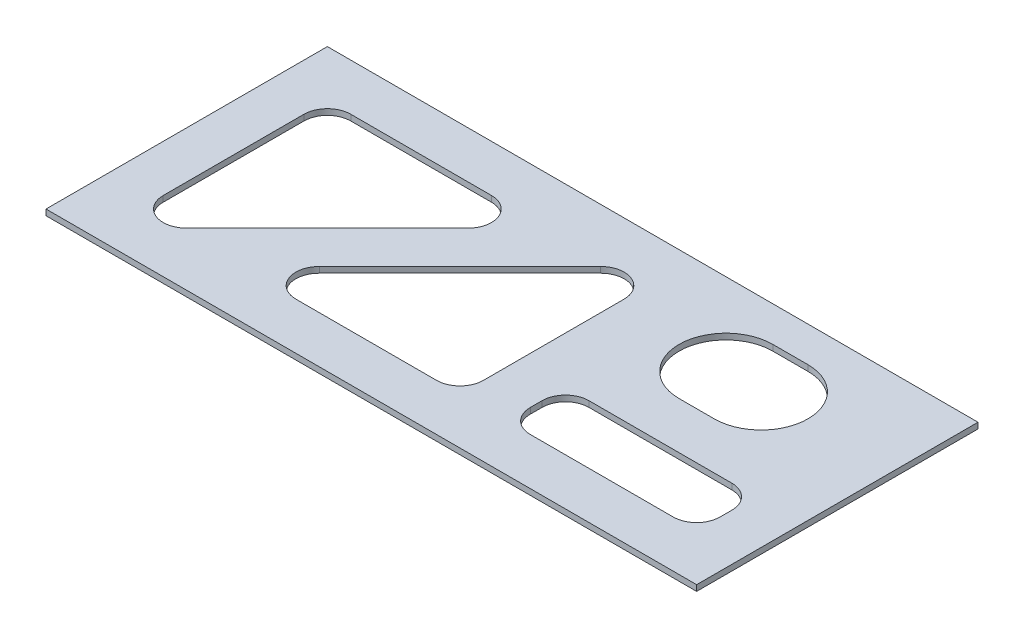
SolidWorks part; units mm, degrees
material "ASTM A36 Steel"
ref_plane "Front Plane" through (0, 0, 0) normal (0, 0, 1) x (1, 0, 0)
ref_plane "Top Plane" through (0, 0, 0) normal (0, 1, 0) x (1, 0, 0)
ref_plane "Right Plane" through (0, 0, 0) normal (1, 0, 0) x (0, 0, -1)
sketch "Sketch1" plane through (0, 0, 0) normal (0, 1, 0) x (1, 0, 0)
  line L1 (176.2125, 76.2) -> (-176.2125, 76.2)
  line L2 (176.2125, 76.2) -> (176.2125, -76.2)
  line L3 (176.2125, -76.2) -> (-176.2125, -76.2)
  line L4 (-176.2125, 76.2) -> (-176.2125, -76.2)
  line L5 (176.2125, 76.2) -> (-176.2125, -76.2) construction
  line L6 (176.2125, -76.2) -> (-176.2125, 76.2) construction
  point P0 (0, 0)
  dimension "D1" = 152.4
  dimension "D2" = 352.425
extrude "Boss-Extrude1" add sketch "Sketch1" along normal mid plane 3.175
sketch "Sketch2" plane through (0, 1.5875, 0) normal (0, 1, 0) x (1, 0, 0)
  line L0 (103.1875, 31.75) -> (84.1375, 31.75) construction
  line L1 (103.1875, 6.35) -> (84.1375, 6.35)
  line L2 (103.1875, 57.15) -> (84.1375, 57.15)
  line L4 (176.2125, -76.2) -> (176.2125, 76.2) construction
  line L5 (176.2125, 76.2) -> (-176.2125, 76.2) construction
  line L6 (-138.1125, 50.8) -> (-61.9125, 50.8)
  line L7 (-52.9322, 29.1197) -> (-129.1322, -47.0803)
  line L8 (-150.8125, -38.1) -> (-150.8125, 38.1)
  line L9 (-176.2125, 76.2) -> (-176.2125, -76.2) construction
  line L10 (-66.2705, -50.8) -> (9.9295, -50.8)
  line L11 (22.6295, -38.1) -> (22.6295, 38.1)
  line L12 (0.9493, 47.0803) -> (-75.2507, -29.1197)
  line L13 (-176.2125, -76.2) -> (176.2125, -76.2) construction
  line L14 (60.7295, -50.8) -> (138.1125, -50.8)
  line L15 (150.8125, -38.1) -> (150.8125, -31.75)
  line L16 (138.1125, -19.05) -> (60.7295, -19.05)
  line L17 (48.0295, -31.75) -> (48.0295, -38.1)
  arc A0 (103.1875, 6.35) -> (103.1875, 57.15) centre (103.1875, 31.75) ccw
  arc A1 (84.1375, 57.15) -> (84.1375, 6.35) centre (84.1375, 31.75) ccw
  arc A2 (-61.9125, 50.8) -> (-52.9322, 29.1197) centre (-61.9125, 38.1) cw
  arc A3 (-129.1322, -47.0803) -> (-150.8125, -38.1) centre (-138.1125, -38.1) cw
  arc A4 (-150.8125, 38.1) -> (-138.1125, 50.8) centre (-138.1125, 38.1) cw
  arc A5 (9.9295, -50.8) -> (22.6295, -38.1) centre (9.9295, -38.1) ccw
  arc A6 (22.6295, 38.1) -> (0.9493, 47.0803) centre (9.9295, 38.1) ccw
  arc A7 (-75.2507, -29.1197) -> (-66.2705, -50.8) centre (-66.2705, -38.1) ccw
  arc A8 (138.1125, -50.8) -> (150.8125, -38.1) centre (138.1125, -38.1) ccw
  arc A9 (150.8125, -31.75) -> (138.1125, -19.05) centre (138.1125, -31.75) ccw
  arc A10 (60.7295, -19.05) -> (48.0295, -31.75) centre (60.7295, -31.75) ccw
  arc A11 (48.0295, -38.1) -> (60.7295, -50.8) centre (60.7295, -38.1) ccw
  point P2 (93.6625, 31.75)
  point P31 (-138.1125, -50.8)
  point P32 (9.9295, 50.8)
  dimension "D2" = 25.4
  dimension "D7" = 12.7
  dimension "D9" = 25.4
  dimension "D1" = 19.05
  dimension "D3" = 44.45
  dimension "D4" = 82.55
  dimension "D5" = 25.4
  dimension "D6" = 25.4
  dimension "D8" = 45
  dimension "D10" = 25.4
  dimension "D11" = 25.4
  dimension "D12" = 25.4
  dimension "D13" = 25.4
extrude "Cut-Extrude1" cut sketch "Sketch2" against normal through all
